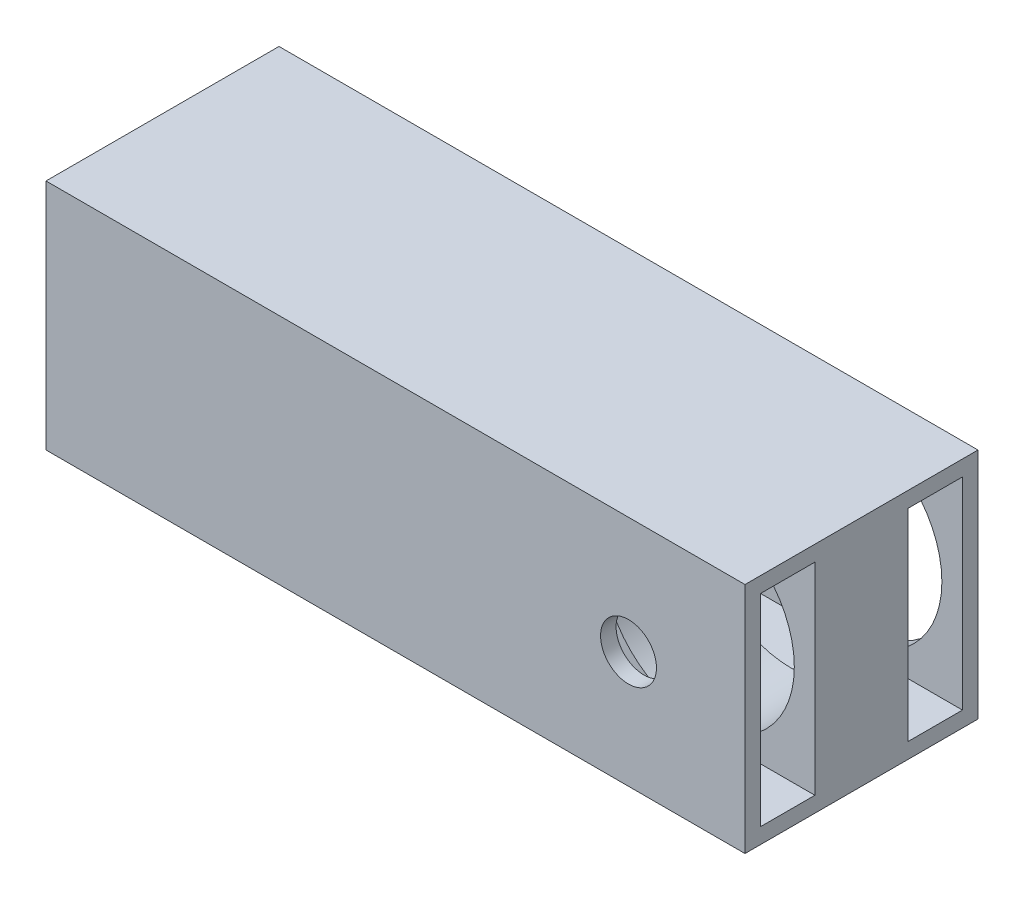
SolidWorks part; units mm, degrees
ref_plane "Front Plane" through (0, 0, 0) normal (0, 0, 1) x (1, 0, 0)
ref_plane "Top Plane" through (0, 0, 0) normal (0, 1, 0) x (1, 0, 0)
ref_plane "Right Plane" through (0, 0, 0) normal (1, 0, 0) x (0, 0, -1)
sketch "Sketch1" plane through (0, 0, 0) normal (1, 0, 0) x (0, 0, -1)
  line L1 (-15, -15) -> (15, -15)
  line L2 (-15, -15) -> (-15, 15)
  line L3 (-15, 15) -> (15, 15)
  line L4 (15, -15) -> (15, 15)
  line L5 (-15, -15) -> (15, 15) construction
  line L6 (-15, 15) -> (15, -15) construction
  line L11 (-5.1844, 5.1844) -> (5.1844, -5.1844) construction
  line L12 (-5.1844, -5.1844) -> (5.1844, 5.1844) construction
  line L13 (-13, 13) -> (-6, 13)
  line L14 (-13, 13) -> (-13, -13)
  line L15 (-13, -13) -> (-6, -13)
  line L16 (-6, 13) -> (-6, -13)
  line L17 (13, 13) -> (6, 13)
  line L18 (13, 13) -> (13, -13)
  line L19 (13, -13) -> (6, -13)
  line L20 (6, 13) -> (6, -13)
  point P0 (0, 0)
  point P7 (0, 0)
  dimension "D1" = 30
  dimension "D2" = 30
  dimension "D3" = 2
  dimension "D4" = 7
  dimension "D5" = 2
  dimension "D6" = 7
  dimension "D7" = 2
  dimension "D8" = 2
extrude "Boss-Extrude3" add sketch "Sketch1" along normal blind 90
sketch "Sketch6" plane through (0, 0, -15) normal (0, 0, -1) x (-1, 0, 0)
  line L0 (-90, -15) -> (-90, 15) construction
  circle A0 centre (-75, 0) radius 12.35
  dimension "D2" = 24.7
  dimension "D1" = 15
extrude "Cut-Extrude5" cut sketch "Sketch6" against normal blind 23
sketch "Sketch8" plane through (0, 0, 15) normal (0, 0, 1) x (1, 0, 0)
  line L0 (90, 15) -> (90, -15) construction
  circle A0 centre (75, 0) radius 3.6
  dimension "D2" = 7.2
  dimension "D1" = 15
extrude "Cut-Extrude6" cut sketch "Sketch8" against normal blind 17
